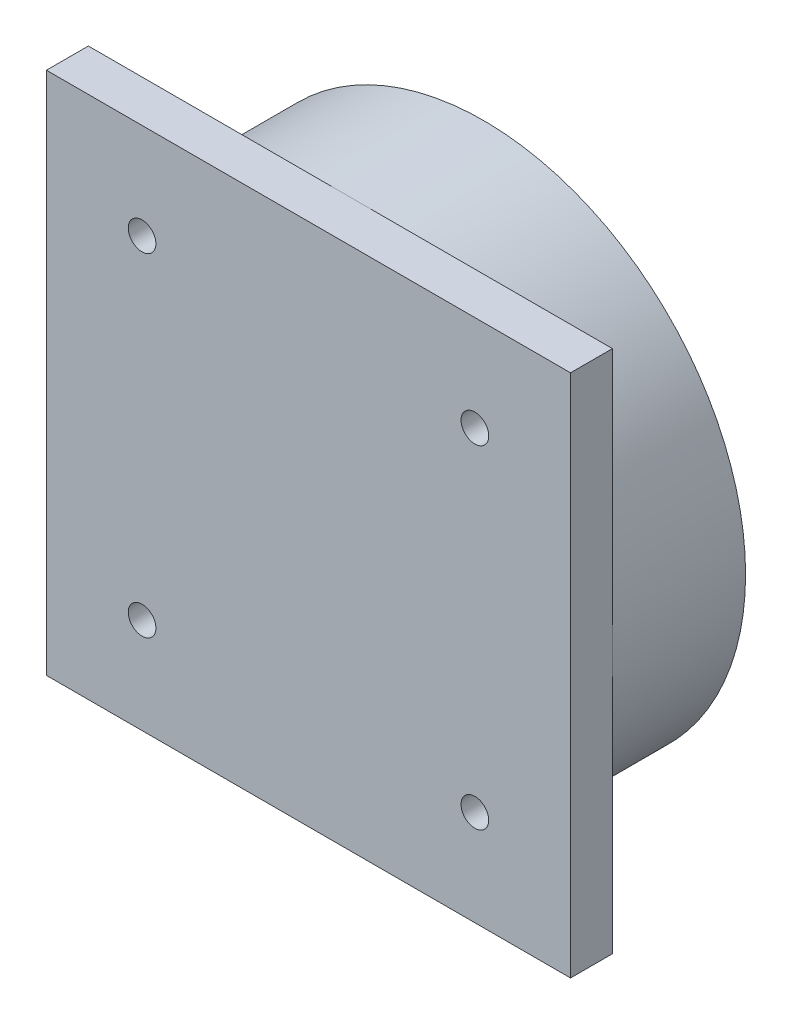
SolidWorks part; units mm, degrees
ref_plane "Front Plane" through (0, 0, 0) normal (0, 0, 1) x (1, 0, 0)
ref_plane "Top Plane" through (0, 0, 0) normal (0, 1, 0) x (1, 0, 0)
ref_plane "Right Plane" through (0, 0, 0) normal (1, 0, 0) x (0, 0, -1)
sketch "Sketch1" plane through (0, 0, 0) normal (0, 0, 1) x (1, 0, 0)
  circle A0 centre (0, 0) radius 25
  dimension "D1" = 50
extrude "Boss-Extrude1" add sketch "Sketch1" along normal blind 12.7
sketch "Sketch2" plane through (0, 0, 12.7) normal (0, 0, 1) x (1, 0, 0)
  line L0 (-25, -25) -> (25, 25) construction
  line L1 (-25, 25) -> (25, 25)
  line L2 (-25, 25) -> (-25, -25)
  line L3 (-25, -25) -> (25, -25)
  line L4 (25, 25) -> (25, -25)
  line L5 (-25, 25) -> (25, -25) construction
  line L6 (0, 0) -> (0, 16.6497) construction
  dimension "D1" = 50
  dimension "D2" = 50
extrude "Boss-Extrude2" add sketch "Sketch2" along normal blind 4
sketch "Sketch3" plane through (0, 0, 16.7) normal (0, 0, 1) x (1, 0, 0)
  line L1 (-15.875, 15.875) -> (15.875, 15.875) construction
  line L2 (15.875, 15.875) -> (15.875, -15.875) construction
  line L3 (15.875, -15.875) -> (-15.875, -15.875) construction
  line L4 (-15.875, -15.875) -> (-15.875, 15.875) construction
  line L5 (-15.875, 15.875) -> (15.875, -15.875) construction
  line L6 (0, 0) -> (-3.1518, -3.1518) construction
  circle A0 centre (-15.875, 15.875) radius 1.32
  circle A1 centre (15.875, 15.875) radius 1.32
  circle A2 centre (15.875, -15.875) radius 1.32
  circle A3 centre (-15.875, -15.875) radius 1.32
  dimension "D1" = 2.64
  dimension "D4" = 31.75
  dimension "D5" = 31.75
  dimension "D2" = 2
  dimension "D3" = 2
extrude "Cut-Extrude1" cut sketch "Sketch3" against normal through all
